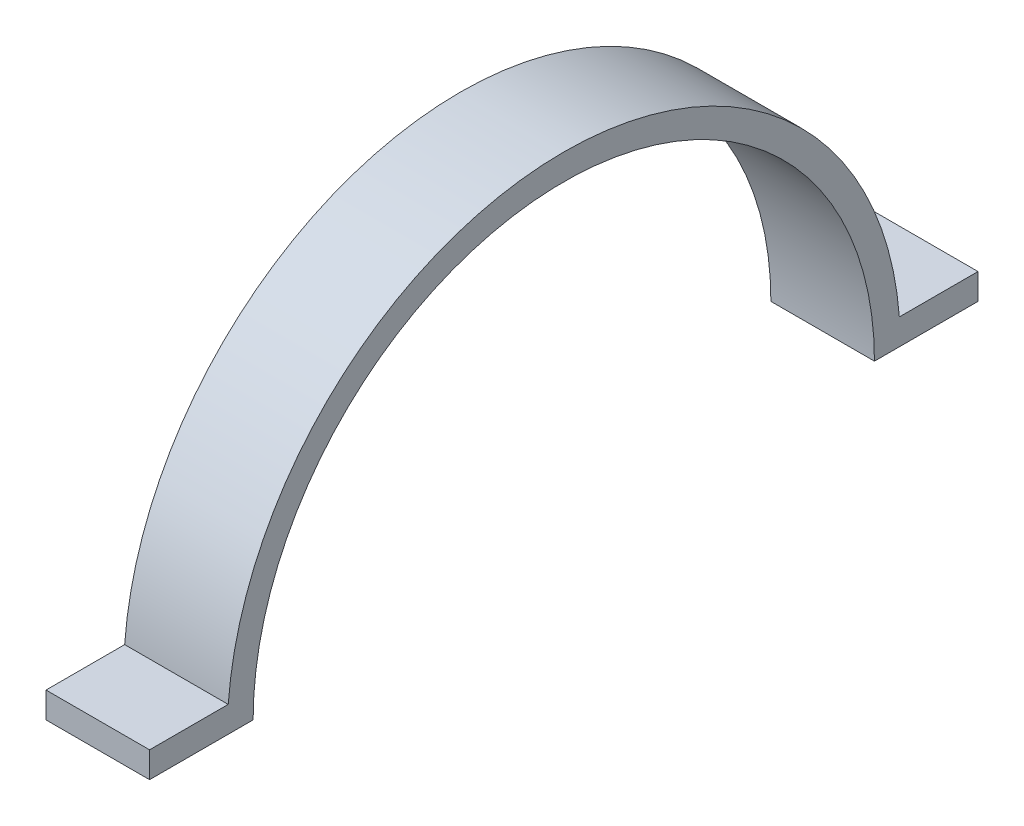
SolidWorks part; units mm, degrees
ref_plane "Front Plane" through (0, 0, 0) normal (0, 0, 1) x (1, 0, 0)
ref_plane "Top Plane" through (0, 0, 0) normal (0, 1, 0) x (1, 0, 0)
ref_plane "Right Plane" through (0, 0, 0) normal (1, 0, 0) x (0, 0, -1)
sketch "Sketch1" plane through (0, 0, 0) normal (1, 0, 0) x (0, 0, -1)
  line L0 (0, -27.2699) -> (0, 27.2699) construction
  line L1 (-30, 0) -> (30, 0) construction
  line L2 (-30, 0) -> (-40, 0)
  line L3 (30, 0) -> (40, 0)
  line L4 (32.4037, 2.5) -> (40, 2.5)
  line L5 (-32.4037, 2.5) -> (-40, 2.5)
  line L6 (-40, 2.5) -> (-40, 0)
  line L7 (40, 2.5) -> (40, 0)
  arc A0 (30, 0) -> (-30, 0) centre (0, 0) ccw
  arc A1 (32.4037, 2.5) -> (-32.4037, 2.5) centre (0, 0) ccw
  point P4 (0, 0)
  point P8 (0, 0)
  point P9 (0, 0)
  dimension "D1" = 60
  dimension "D2" = 10
  dimension "D3" = 2.5
extrude "Boss-Extrude1" add sketch "Sketch1" along normal blind 10
